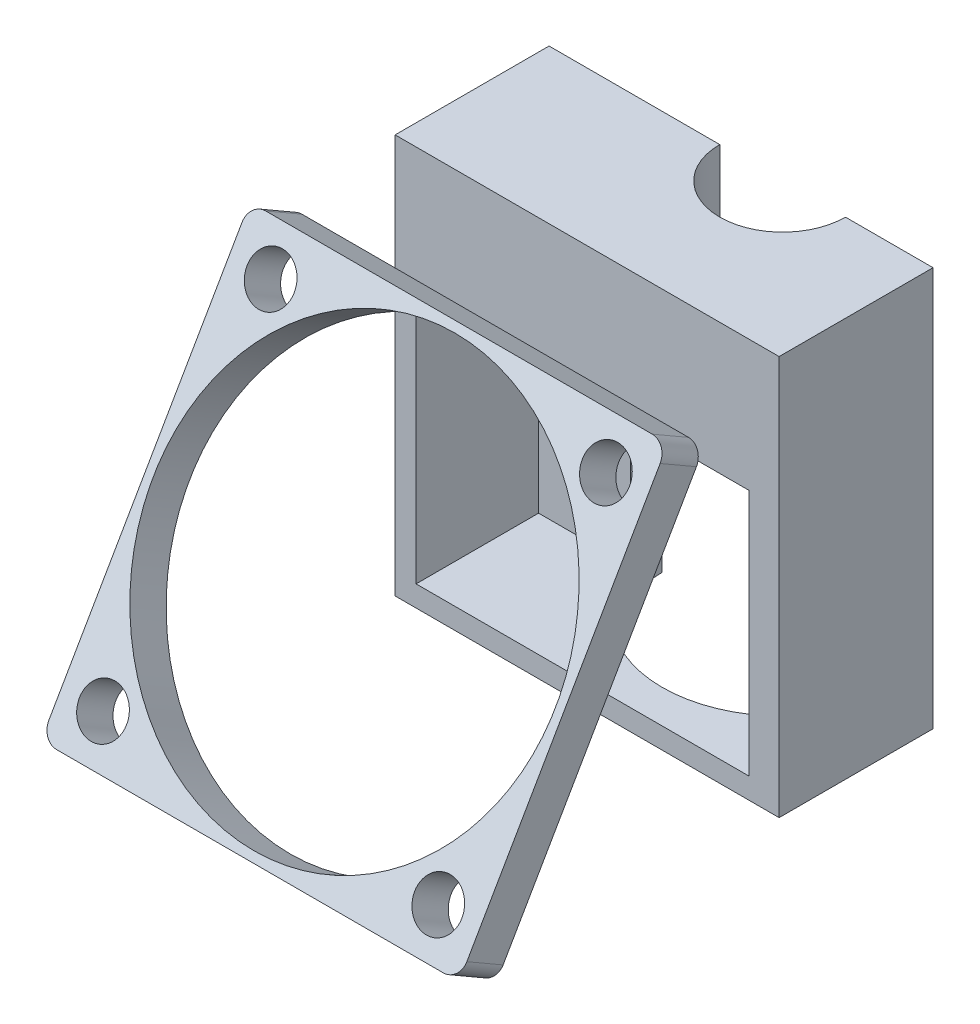
SolidWorks part; units mm, degrees
ref_plane "Front Plane" through (0, 0, 0) normal (0, 0, 1) x (1, 0, 0)
ref_plane "Top Plane" through (0, 0, 0) normal (0, 1, 0) x (1, 0, 0)
ref_plane "Right Plane" through (0, 0, 0) normal (1, 0, 0) x (0, 0, -1)
sketch "Sketch1" plane through (0, -168.6472, 0) normal (0, 1, 0) x (1, 0, 0)
  line L0 (-33.4072, -166.8592) -> (-45.4072, -166.8592) construction
  line L1 (-33.4072, -166.8592) -> (-25.0496, -166.8592)
  line L2 (-25.0496, -166.8592) -> (-25.0496, -172.0508)
  line L3 (-25.0496, -172.0508) -> (-25.0496, -181.5508)
  line L4 (-25.0496, -181.5508) -> (-61.6994, -181.5508)
  line L5 (-61.6994, -181.5508) -> (-61.6994, -166.8592)
  line L6 (-61.6994, -166.8592) -> (-45.4072, -166.8592)
  arc A0 (-45.4072, -166.8592) -> (-33.4072, -166.8592) centre (-39.4072, -166.8592) ccw
  arc A1 (-33.4072, -166.8592) -> (-45.4072, -166.8592) centre (-39.4072, -166.8592) ccw construction
  dimension "D1" = 9.5
extrude "Boss-Extrude1" add sketch "Sketch1" against normal up to surface (6 mm away)
sketch "Sketch2" plane through (0, -174.6472, 0) normal (0, -1, 0) x (1, 0, 0)
  line L0 (-45.4072, 166.8592) -> (-33.4072, 166.8592) construction
  line L1 (-47.4072, 166.8592) -> (-61.6994, 166.8592)
  line L2 (-61.6994, 166.8592) -> (-61.6994, 181.5508)
  line L3 (-61.6994, 181.5508) -> (-25.0496, 181.5508)
  line L4 (-25.0496, 181.5508) -> (-25.0496, 166.8592)
  line L5 (-25.0496, 166.8592) -> (-31.4072, 166.8592)
  arc A0 (-31.4072, 166.8592) -> (-47.4072, 166.8592) centre (-39.4072, 166.8592) ccw
  arc A1 (-47.4072, 166.8592) -> (-31.4072, 166.8592) centre (-39.4072, 166.8592) ccw construction
extrude "Boss-Extrude2" add sketch "Sketch2" along normal up to surface (3 mm away)
sketch "Sketch3" plane through (0, -177.6472, 0) normal (0, -1, 0) x (1, 0, 0)
  line L0 (-45.4072, 166.8592) -> (-33.4072, 166.8592) construction
  line L1 (-45.4072, 166.8592) -> (-61.6994, 166.8592)
  line L2 (-61.6994, 166.8592) -> (-61.6994, 181.5508)
  line L3 (-61.6994, 181.5508) -> (-25.0496, 181.5508)
  line L4 (-25.0496, 181.5508) -> (-25.0496, 166.8592)
  line L5 (-25.0496, 166.8592) -> (-33.4072, 166.8592)
  arc A0 (-33.4072, 166.8592) -> (-45.4072, 166.8592) centre (-39.4072, 166.8592) ccw
  arc A1 (-45.4072, 166.8592) -> (-33.4072, 166.8592) centre (-39.4072, 166.8592) ccw construction
extrude "Boss-Extrude3" add sketch "Sketch3" along normal up to surface (1.5 mm away)
sketch "Sketch4" plane through (0, -179.1472, 0) normal (0, -1, 0) x (1, 0, 0)
  line L0 (-45.4072, 166.8592) -> (-33.4072, 166.8592) construction
  line L1 (-47.4072, 166.8592) -> (-61.6994, 166.8592)
  line L2 (-61.6994, 166.8592) -> (-61.6994, 181.5508)
  line L3 (-61.6994, 181.5508) -> (-25.0496, 181.5508)
  line L4 (-25.0496, 181.5508) -> (-25.0496, 166.8592)
  line L5 (-25.0496, 166.8592) -> (-31.4072, 166.8592)
  arc A0 (-31.4072, 166.8592) -> (-47.4072, 166.8592) centre (-39.4072, 166.8592) ccw
  arc A1 (-47.4072, 166.8592) -> (-31.4072, 166.8592) centre (-39.4072, 166.8592) ccw construction
extrude "Boss-Extrude4" add sketch "Sketch4" along normal up to surface (1 mm away)
sketch "Sketch5" plane through (0, -180.1472, 0) normal (0, -1, 0) x (1, 0, 0)
  line L0 (-45.4072, 166.8592) -> (-33.4072, 166.8592) construction
  line L1 (-45.4072, 166.8592) -> (-61.6994, 166.8592)
  line L2 (-61.6994, 166.8592) -> (-61.6994, 181.5508)
  line L3 (-61.6994, 181.5508) -> (-25.0496, 181.5508)
  line L4 (-25.0496, 181.5508) -> (-25.0496, 166.8592)
  line L5 (-25.0496, 166.8592) -> (-33.4072, 166.8592)
  arc A0 (-33.4072, 166.8592) -> (-45.4072, 166.8592) centre (-39.4072, 166.8592) ccw
  arc A1 (-45.4072, 166.8592) -> (-33.4072, 166.8592) centre (-39.4072, 166.8592) ccw construction
extrude "Boss-Extrude5" add sketch "Sketch5" along normal up to surface (1 mm away)
sketch "Sketch6" plane through (0, -181.1472, 0) normal (0, -1, 0) x (1, 0, 0)
  line L0 (-50.9072, 149.5618) -> (-50.9072, 166.8592) construction
  line L1 (-61.6994, 166.8592) -> (-50.9072, 166.8592)
  line L2 (-61.6994, 166.8592) -> (-61.6994, 169.8592)
  line L3 (-61.6994, 169.8592) -> (-50.9072, 169.8592)
  line L4 (-50.9072, 166.8592) -> (-50.9072, 169.8592)
  line L5 (-25.0496, 181.5508) -> (-25.0496, 166.8592) construction
  line L6 (-27.9072, 166.8592) -> (-25.0496, 166.8592)
  line L7 (-27.9072, 166.8592) -> (-27.9072, 169.8592)
  line L8 (-27.9072, 169.8592) -> (-25.0496, 169.8592)
  line L9 (-25.0496, 166.8592) -> (-25.0496, 169.8592)
  dimension "D1" = 3
extrude "Boss-Extrude6" add sketch "Sketch6" along normal up to surface (25.6159 mm away)
sketch "Sketch7" plane through (0, -206.7631, 0) normal (0, -1, 0) x (1, 0, 0)
  line L0 (-50.9072, 166.8592) -> (-27.9072, 166.8592) construction
  line L1 (-53.7647, 166.8592) -> (-50.9072, 166.8592)
  line L2 (-27.9072, 166.8592) -> (-25.0496, 166.8592)
  arc A0 (-27.9072, 166.8592) -> (-50.9072, 166.8592) centre (-39.4072, 166.8592) ccw
  arc A1 (-25.0496, 166.8592) -> (-53.7647, 166.8592) centre (-39.4072, 166.8592) ccw
  arc A2 (-53.7647, 166.8592) -> (-25.0496, 166.8592) centre (-39.4072, 166.8592) ccw construction
  arc A3 (-50.9072, 166.8592) -> (-27.9072, 166.8592) centre (-39.4072, 166.8592) ccw construction
extrude "Boss-Extrude7" add sketch "Sketch7" against normal up to surface (2 mm away) contours A1 L1 A0 L2
sketch "Sketch8" plane through (0, 0, 181.5508) normal (0, 0, 1) x (1, 0, 0)
  line L0 (-27.9072, -204.7631) -> (-25.3665, -204.7631) construction
  line L1 (-25.3665, -204.7631) -> (-25.3665, -206.7631) construction
  line L2 (-25.3665, -206.7631) -> (-25.0496, -206.7631) construction
  line L3 (-25.0496, -206.7631) -> (-25.0496, -181.1472) construction
  line L4 (-25.0496, -181.1472) -> (-27.9072, -181.1472) construction
  line L5 (-27.9072, -181.1472) -> (-27.9072, -204.7631) construction
  line L6 (-61.6994, -206.7631) -> (-53.4478, -206.7631) construction
  line L7 (-53.4478, -206.7631) -> (-53.4478, -204.7631) construction
  line L8 (-53.4478, -204.7631) -> (-50.9072, -204.7631) construction
  line L9 (-50.9072, -204.7631) -> (-50.9072, -181.1472) construction
  line L10 (-50.9072, -181.1472) -> (-61.6994, -181.1472) construction
  line L11 (-61.6994, -181.1472) -> (-61.6994, -206.7631) construction
  line L12 (-27.9072, -204.7631) -> (-25.3665, -204.7631) construction
  line L13 (-25.3665, -204.7631) -> (-25.3665, -206.7631) construction
  line L14 (-25.3665, -206.7631) -> (-25.0496, -206.7631)
  line L15 (-25.0496, -206.7631) -> (-25.0496, -181.1472)
  line L16 (-25.0496, -181.1472) -> (-27.9072, -181.1472)
  line L17 (-27.9072, -181.1472) -> (-27.9072, -204.7631)
  line L18 (-61.6994, -206.7631) -> (-53.4478, -206.7631)
  line L19 (-53.4478, -206.7631) -> (-53.4478, -204.7631) construction
  line L20 (-53.4478, -204.7631) -> (-50.9072, -204.7631) construction
  line L21 (-50.9072, -204.7631) -> (-50.9072, -181.1472) construction
  line L22 (-59.6994, -181.1472) -> (-61.6994, -181.1472)
  line L23 (-61.6994, -181.1472) -> (-61.6994, -206.7631)
  line L24 (-53.4478, -204.7631) -> (-50.9072, -204.7631) construction
  line L25 (-50.9072, -204.7631) -> (-27.9072, -204.7631)
  line L26 (-53.4478, -204.7631) -> (-53.4478, -206.7631) construction
  line L27 (-53.4478, -206.7631) -> (-25.3665, -206.7631)
  line L28 (-25.3665, -204.7631) -> (-25.3665, -206.7631) construction
  line L29 (-27.9072, -204.7631) -> (-25.3665, -204.7631) construction
  line L30 (-59.6994, -204.7631) -> (-61.6994, -204.7631) construction
  line L31 (-50.9072, -181.1472) -> (-59.6994, -181.1472) construction
  line L32 (-50.9072, -181.1472) -> (-50.9072, -204.7631) construction
  line L33 (-50.9072, -204.7631) -> (-59.6994, -204.7631)
  line L34 (-59.6994, -181.1472) -> (-59.6994, -204.7631)
  line L35 (-59.6994, -204.7631) -> (-59.6994, -206.7631) construction
  line L36 (-50.9072, -181.1472) -> (-59.6994, -181.1472) construction
extrude "Boss-Extrude8" add sketch "Sketch8" against normal up to surface (11.6916 mm away) up to face at (-55.3515, -197.5578, 169.8592)
sketch "Sketch9" plane through (0, -206.7631, 0) normal (0, -1, 0) x (1, 0, 0)
  line L0 (-50.9072, 166.8592) -> (-27.9072, 166.8592) construction
  line L1 (-50.9072, 166.8592) -> (-27.9072, 166.8592)
  arc A0 (-27.9072, 166.8592) -> (-50.9072, 166.8592) centre (-39.4072, 166.8592) ccw
  arc A1 (-50.9072, 166.8592) -> (-27.9072, 166.8592) centre (-39.4072, 166.8592) ccw construction
extrude "Cut-Extrude1" cut sketch "Sketch9" against normal up to surface (2 mm away) up to face at (-44.4802, -204.7631, 172.0354)
sketch "Sketch10" plane through (0, 40.5794, 70.2856) normal (0, -0.5, -0.866) x (-1, 0, 0)
  line L0 (26.7496, -279.6935) -> (31.2496, -279.6935) construction
  line L1 (58.7496, -279.6935) -> (63.2496, -279.6935) construction
  line L2 (26.7496, -247.6935) -> (31.2496, -247.6935) construction
  line L3 (58.7496, -247.6935) -> (63.2496, -247.6935) construction
  line L4 (26.5496, -283.6435) -> (63.4496, -283.6435)
  line L5 (64.9496, -282.1435) -> (64.9496, -245.2435)
  line L6 (63.4496, -243.7435) -> (26.5496, -243.7435)
  line L7 (25.0496, -245.2435) -> (25.0496, -282.1435)
  line L8 (25.4446, -263.6935) -> (64.5546, -263.6935) construction
  arc A0 (26.7496, -279.6935) -> (31.2496, -279.6935) centre (28.9996, -279.6935) ccw construction
  arc A1 (31.2496, -279.6935) -> (26.7496, -279.6935) centre (28.9996, -279.6935) ccw construction
  arc A2 (26.7496, -279.6935) -> (31.2496, -279.6935) centre (28.9996, -279.6935) ccw
  arc A3 (31.2496, -279.6935) -> (26.7496, -279.6935) centre (28.9996, -279.6935) ccw
  arc A4 (58.7496, -279.6935) -> (63.2496, -279.6935) centre (60.9996, -279.6935) ccw construction
  arc A5 (63.2496, -279.6935) -> (58.7496, -279.6935) centre (60.9996, -279.6935) ccw construction
  arc A6 (58.7496, -279.6935) -> (63.2496, -279.6935) centre (60.9996, -279.6935) ccw
  arc A7 (63.2496, -279.6935) -> (58.7496, -279.6935) centre (60.9996, -279.6935) ccw
  arc A8 (26.7496, -247.6935) -> (31.2496, -247.6935) centre (28.9996, -247.6935) ccw construction
  arc A9 (31.2496, -247.6935) -> (26.7496, -247.6935) centre (28.9996, -247.6935) ccw construction
  arc A10 (26.7496, -247.6935) -> (31.2496, -247.6935) centre (28.9996, -247.6935) ccw
  arc A11 (31.2496, -247.6935) -> (26.7496, -247.6935) centre (28.9996, -247.6935) ccw
  arc A12 (63.2496, -247.6935) -> (58.7496, -247.6935) centre (60.9996, -247.6935) ccw construction
  arc A13 (58.7496, -247.6935) -> (63.2496, -247.6935) centre (60.9996, -247.6935) ccw construction
  arc A14 (63.2496, -247.6935) -> (58.7496, -247.6935) centre (60.9996, -247.6935) ccw
  arc A15 (58.7496, -247.6935) -> (63.2496, -247.6935) centre (60.9996, -247.6935) ccw
  arc A16 (25.0496, -282.1435) -> (26.5496, -283.6435) centre (26.5496, -282.1435) ccw construction
  arc A17 (63.4496, -283.6435) -> (64.9496, -282.1435) centre (63.4496, -282.1435) ccw construction
  arc A18 (64.9496, -245.2435) -> (63.4496, -243.7435) centre (63.4496, -245.2435) ccw construction
  arc A19 (26.5496, -243.7435) -> (25.0496, -245.2435) centre (26.5496, -245.2435) ccw construction
  arc A20 (25.0496, -282.1435) -> (26.5496, -283.6435) centre (26.5496, -282.1435) ccw
  arc A21 (63.4496, -283.6435) -> (64.9496, -282.1435) centre (63.4496, -282.1435) ccw
  arc A22 (64.9496, -245.2435) -> (63.4496, -243.7435) centre (63.4496, -245.2435) ccw
  arc A23 (26.5496, -243.7435) -> (25.0496, -245.2435) centre (26.5496, -245.2435) ccw
  circle A24 centre (44.9996, -263.6935) radius 19.1772
  point P30 (0, 0)
  point P34 (0, 0)
  point P36 (44.9996, -263.6935)
extrude "Boss-Extrude9" add sketch "Sketch10" along normal blind 4 separate body
